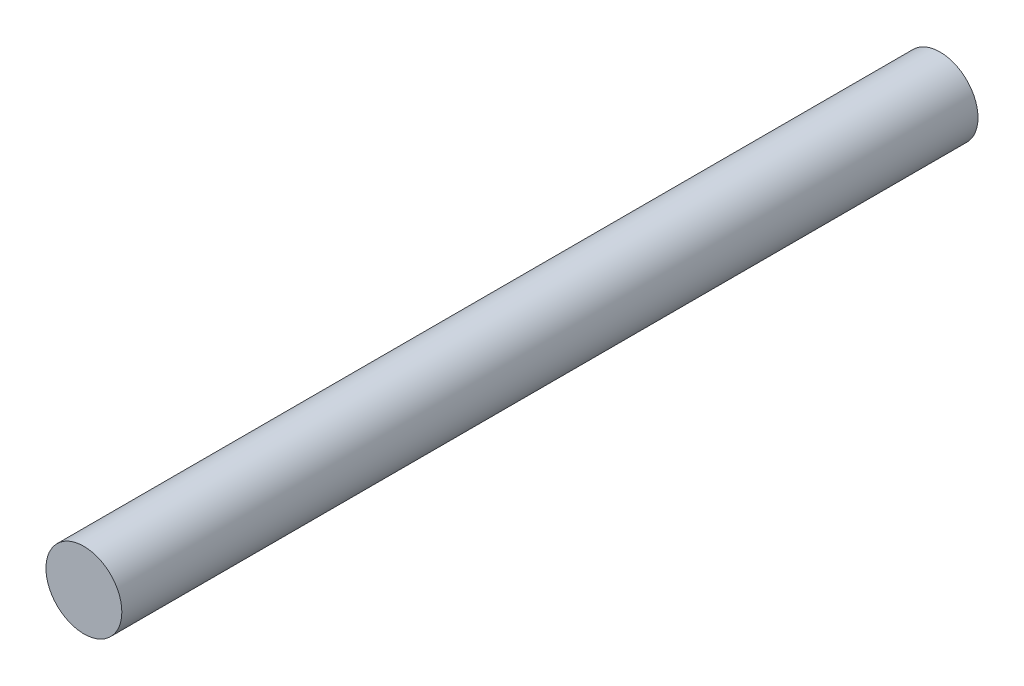
SolidWorks part; units mm, degrees
ref_plane "Front Plane" through (0, 0, 0) normal (0, 0, 1) x (1, 0, 0)
ref_plane "Top Plane" through (0, 0, 0) normal (0, 1, 0) x (1, 0, 0)
ref_plane "Right Plane" through (0, 0, 0) normal (1, 0, 0) x (0, 0, -1)
sketch "Sketch1" plane through (0, 0, 0) normal (0, 0, 1) x (1, 0, 0)
  circle A0 centre (0, 0) radius 3.3782
  dimension "D1" = 6.7564
extrude "Boss-Extrude1" add sketch "Sketch1" along normal mid plane 76.2
